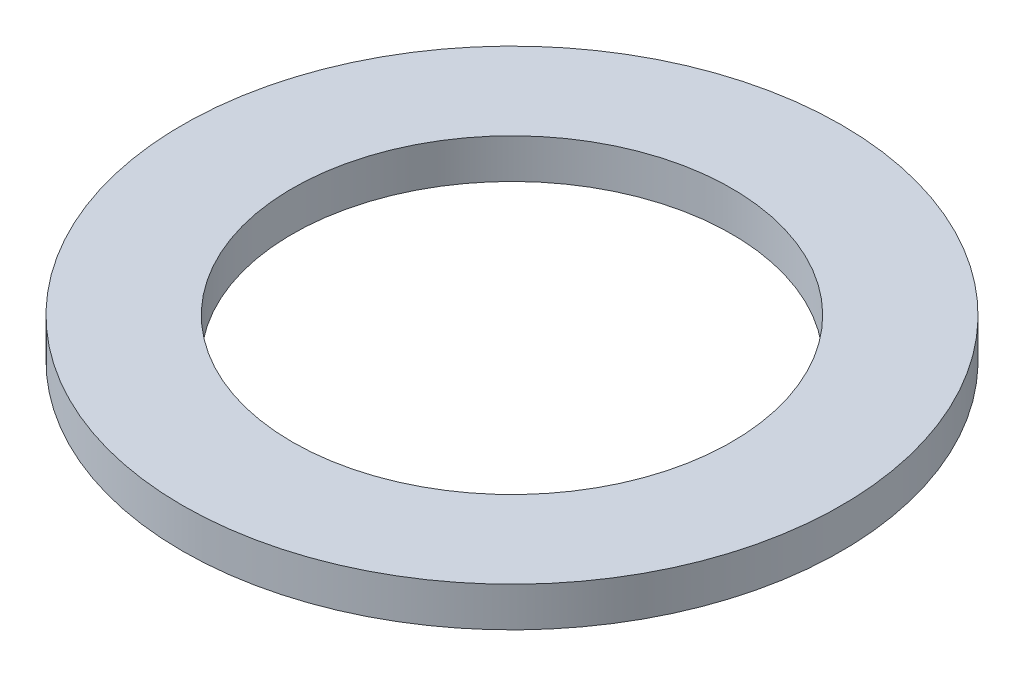
SolidWorks part; units mm, degrees
material "AISI 304"
ref_plane "Ön Düzlem" through (0, 0, 0) normal (0, 0, 1) x (1, 0, 0)
ref_plane "Üst Düzlem" through (0, 0, 0) normal (0, 1, 0) x (1, 0, 0)
ref_plane "Sağ Düzlem" through (0, 0, 0) normal (1, 0, 0) x (0, 0, -1)
sketch "Çizim1" plane through (0, 0, 0) normal (0, 1, 0) x (1, 0, 0)
  circle A0 centre (0, 0) radius 7.5
  circle A1 centre (0, 0) radius 5
  dimension "D1" = 15
  dimension "D2" = 10
extrude "Yükseklik-Ekstrüzyon1" add sketch "Çizim1" along normal blind 0.9
